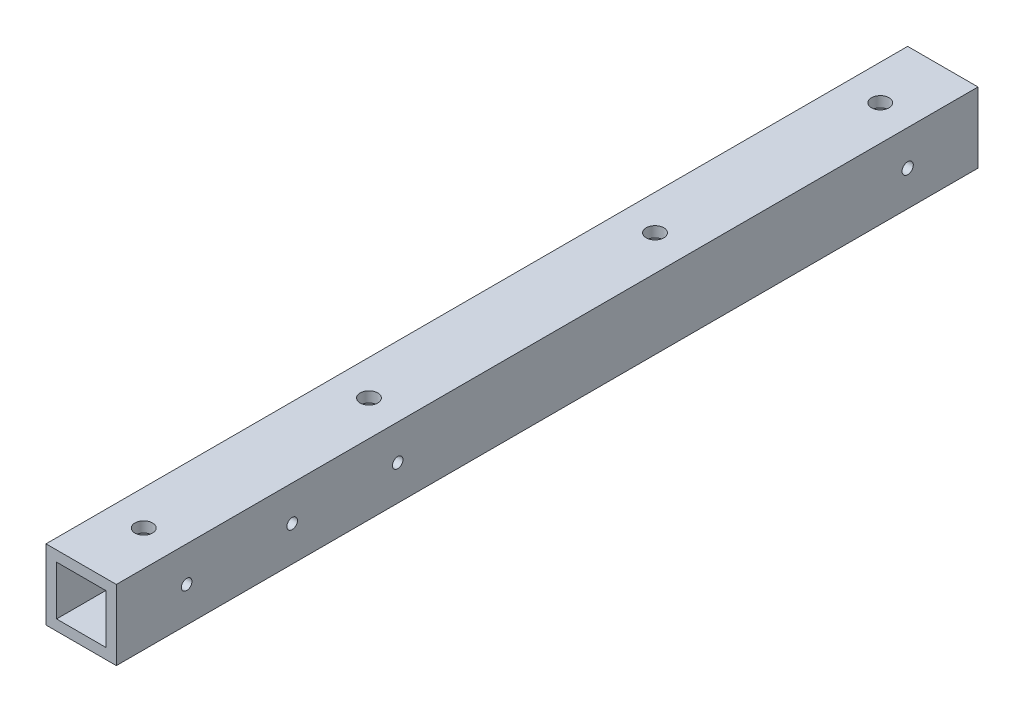
SolidWorks part; units mm, degrees
ref_plane "前视基准面" through (0, 0, 0) normal (0, 0, 1) x (1, 0, 0)
ref_plane "上视基准面" through (0, 0, 0) normal (0, 1, 0) x (1, 0, 0)
ref_plane "右视基准面" through (0, 0, 0) normal (1, 0, 0) x (0, 0, -1)
other "Configuration Table"
sketch "草图1" plane through (0, 0, 0) normal (0, 0, 1) x (1, 0, 0)
  line L0 (-9.3333, 11.0061) -> (-9.3333, -8.9939)
  line L1 (-9.3333, 11.0061) -> (10.6667, 11.0061)
  line L2 (-9.3333, -8.9939) -> (10.6667, -8.9939)
  line L3 (10.6667, 11.0061) -> (10.6667, -8.9939)
  dimension "D1" = 20
  dimension "D2" = 20
extrude "凸台-拉伸1" add sketch "草图1" along normal blind 245
sketch "草图2" plane through (0, 0, 0) normal (0, 0, -1) x (-1, 0, 0)
  line L0 (-10.6667, -8.9939) -> (-10.6667, 11.0061) construction
  line L1 (-7.6667, 8.0061) -> (6.3333, 8.0061)
  line L2 (-7.6667, 8.0061) -> (-7.6667, -5.9939)
  line L3 (-7.6667, -5.9939) -> (6.3333, -5.9939)
  line L4 (6.3333, 8.0061) -> (6.3333, -5.9939)
  line L5 (9.3333, 11.0061) -> (9.3333, -8.9939) construction
  line L6 (9.3333, -8.9939) -> (-10.6667, -8.9939) construction
  line L7 (-10.6667, 11.0061) -> (9.3333, 11.0061) construction
  dimension "D1" = 3
  dimension "D2" = 3
  dimension "D3" = 3
  dimension "D4" = 3
extrude "切除-拉伸1" cut sketch "草图2" against normal through all
sketch "草图3" plane through (-9.3333, 0, 0) normal (-1, 0, 0) x (0, 0, 1)
  circle A0 centre (225, 1.0061) radius 1.5
  circle A1 centre (195, 1.0061) radius 1.5
  circle A2 centre (165, 1.0061) radius 1.5
  circle A3 centre (20, 1.0061) radius 1.6
  dimension "D1" = 3.2
extrude "切除-拉伸2" cut sketch "草图3" against normal blind 80
sketch "草图4" plane through (0, 11.0061, 0) normal (0, 1, 0) x (1, 0, 0)
  circle A0 centre (0.6667, -17.7882) radius 2.5
  circle A1 centre (0.6667, -81.8331) radius 2.5
  circle A2 centre (0.6667, -163.1669) radius 2.5
  circle A3 centre (0.6667, -227.2118) radius 2.5
  point P2 (0.6667, -227.2118)
  dimension "D1" = 5
  dimension "D2" = 5
  dimension "D3" = 5
  dimension "D4" = 5
extrude "切除-拉伸3" cut sketch "草图4" against normal blind 93
